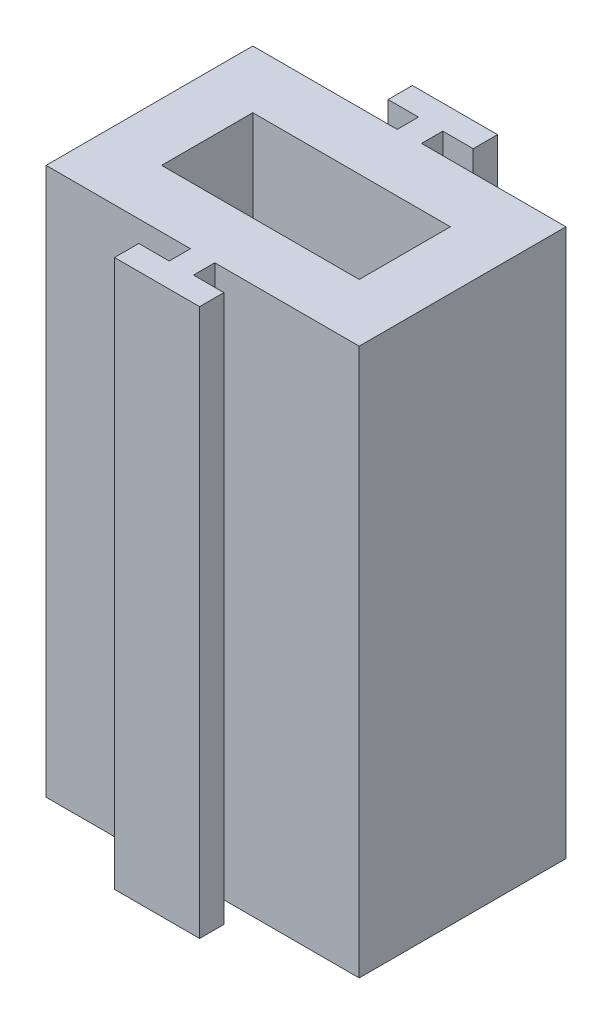
SolidWorks part; units mm, degrees
ref_plane "Front Plane" through (0, 0, 0) normal (0, 0, 1) x (1, 0, 0)
ref_plane "Top Plane" through (0, 0, 0) normal (0, 1, 0) x (1, 0, 0)
ref_plane "Right Plane" through (0, 0, 0) normal (1, 0, 0) x (0, 0, -1)
sketch "Sketch3" plane through (0, 0, 0) normal (0, 1, 0) x (1, 0, 0)
  line L0 (-5.15, 3.4) -> (-5.15, -3.4)
  line L1 (-5.15, -3.4) -> (5.15, -3.4)
  line L2 (-0.5, -4) -> (0.5, -4)
  line L3 (-0.5, -4) -> (-0.5, 4)
  line L4 (-0.5, 4) -> (0.5, 4)
  line L5 (5.15, 3.4) -> (5.15, -3.4)
  line L6 (-1.5, -4) -> (1.5, -4)
  line L7 (0.5, -4) -> (0.5, 4)
  line L8 (-0.5, -4) -> (0.5, 4) construction
  line L9 (-0.5, 4) -> (0.5, -4) construction
  line L10 (-5.25, 3.5) -> (5.25, 3.5)
  line L11 (-5.15, 3.4) -> (5.15, 3.4)
  line L12 (-5.25, 3.5) -> (-5.25, -3.5)
  line L13 (-5.25, -3.5) -> (5.25, -3.5)
  line L14 (5.25, 3.5) -> (5.25, -3.5)
  line L15 (-5.25, 3.5) -> (5.25, -3.5) construction
  line L16 (-5.25, -3.5) -> (5.25, 3.5) construction
  line L17 (-1.5, -4) -> (-1.5, -5)
  line L18 (-1.5, -5) -> (1.5, -5)
  line L19 (1.5, -4) -> (1.5, -5)
  line L20 (-1.5, -4) -> (1.5, -5) construction
  line L21 (-1.5, -5) -> (1.5, -4) construction
  line L22 (-1.5, 5) -> (1.5, 5)
  line L23 (-1.5, 5) -> (-1.5, 4)
  line L24 (-1.5, 4) -> (1.5, 4)
  line L25 (1.5, 5) -> (1.5, 4)
  line L26 (-1.5, 5) -> (1.5, 4) construction
  line L27 (-1.5, 4) -> (1.5, 5) construction
  line L28 (-0.4, -3.9) -> (-0.4, 3.9)
  line L29 (-0.4, 3.9) -> (0.4, 3.9)
  line L30 (0.4, -3.9) -> (0.4, 3.9)
  line L31 (-0.4, -3.9) -> (0.4, -3.9)
  line L32 (-1.4, -4.1) -> (-1.4, -4.9)
  line L33 (-1.4, -4.9) -> (1.4, -4.9)
  line L34 (1.4, -4.1) -> (1.4, -4.9)
  line L35 (-1.4, -4.1) -> (1.4, -4.1)
  line L36 (-1.4, 4.9) -> (-1.4, 4.1)
  line L37 (-1.4, 4.1) -> (1.4, 4.1)
  line L38 (1.4, 4.9) -> (1.4, 4.1)
  line L39 (-1.4, 4.9) -> (1.4, 4.9)
  line L40 (0.4, -3.9) -> (0.4, -4.1)
  line L41 (-0.4, -3.9) -> (-0.4, -4.1)
  line L42 (0.4, 3.9) -> (0.4, 4.1)
  line L43 (-0.4, 3.9) -> (-0.4, 4.1)
  point P2 (0, -4.5)
  point P20 (0, 4.5)
  point P21 (0, 4.5)
  point P30 (0, -4.5)
  point P46 (0, -4)
  dimension "D1" = 0.1
extrude "Boss-Extrude7" add sketch "Sketch3" along normal blind 18 contours L39 L36 L37 L38 | L43 L24 L42 L37 | L43 L29 L42 L24 | L10 L30 L29 L28 | L11 L30 L10 L28 | L1 L30 L11 L28 | L30 L1 L7 L11 | L11 L7 L1 L5 | L1 L28 L11 L3 | L11 L0 L1 L3 | L13 L30 L1 L28 | L28 L31 L30 L13 | L31 L41 L6 L40 | L2 L41 L35 L40 | L35 L32 L33 L34
sketch "Sketch24" plane through (0, 18, 0) normal (0, 1, 0) x (1, 0, 0)
  line L1 (-3.25, -1.5) -> (3.25, -1.5)
  line L2 (-3.25, -1.5) -> (-3.25, 1.5)
  line L3 (-3.25, 1.5) -> (3.25, 1.5)
  line L4 (3.25, -1.5) -> (3.25, 1.5)
  line L5 (-3.25, -1.5) -> (3.25, 1.5) construction
  line L6 (-3.25, 1.5) -> (3.25, -1.5) construction
  point P0 (0, 0)
extrude "Cut-Extrude25" cut sketch "Sketch24" against normal blind 18
